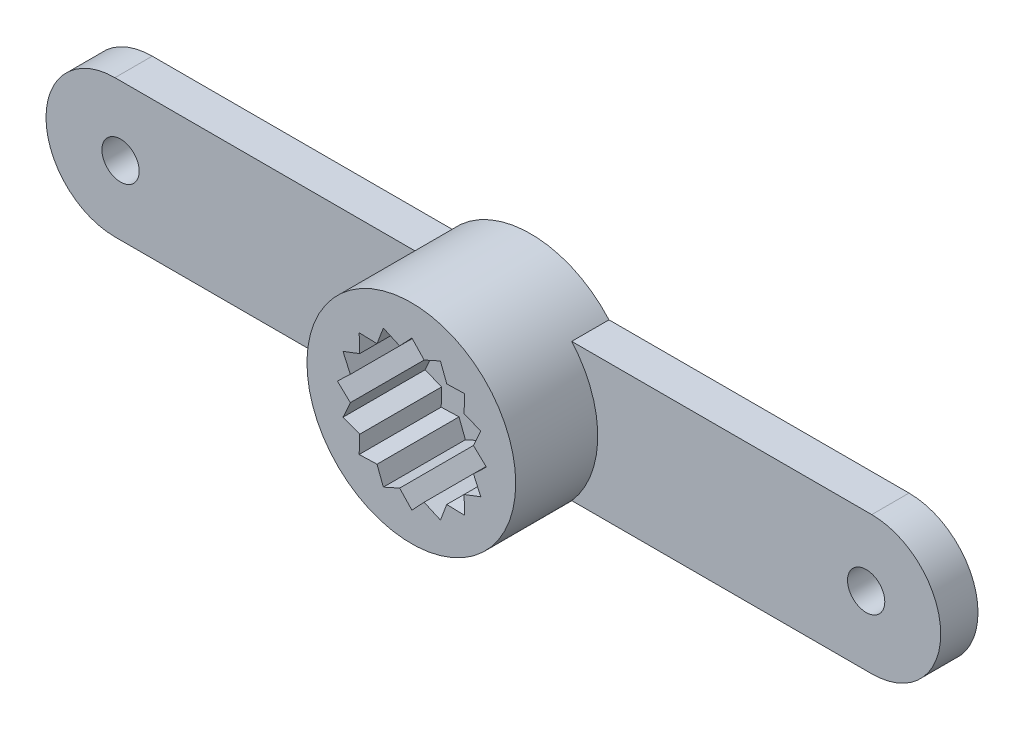
SolidWorks part; units mm, degrees
ref_plane "Front Plane" through (0, 0, 0) normal (0, 0, 1) x (1, 0, 0)
ref_plane "Top Plane" through (0, 0, 0) normal (0, 1, 0) x (1, 0, 0)
ref_plane "Right Plane" through (0, 0, 0) normal (1, 0, 0) x (0, 0, -1)
sketch "Sketch1" plane through (0, 0, 0) normal (0, 0, 1) x (1, 0, 0)
  circle A0 centre (0, 0) radius 2.8
  dimension "D1" = 5.6
extrude "Boss-Extrude1" add sketch "Sketch1" along normal blind 3.2
sketch "Sketch2" plane through (0, 0, 3.2) normal (0, 0, 1) x (1, 0, 0)
  line L0 (0.0147, -0.0147) -> (0.0147, 1.9853) construction
  line L1 (0.0147, -0.0147) -> (0.3432, 1.637) construction
  line L2 (0.0147, -0.0147) -> (-0.3139, 1.637) construction
  line L3 (0.0147, 1.9853) -> (-0.3139, 1.637)
  line L4 (0.0147, 1.9853) -> (0.3432, 1.637)
  line L5 (0.78, 1.8331) -> (0.9502, 1.3855)
  line L6 (0.78, 1.8331) -> (0.3432, 1.637)
  line L7 (1.4289, 1.3996) -> (1.4148, 0.9209)
  line L8 (1.4289, 1.3996) -> (0.9502, 1.3855)
  line L9 (1.8624, 0.7507) -> (1.6663, 0.3139)
  line L10 (1.8624, 0.7507) -> (1.4148, 0.9209)
  line L11 (2.0147, -0.0147) -> (1.6663, -0.3432)
  line L12 (2.0147, -0.0147) -> (1.6663, 0.3139)
  line L13 (1.8624, -0.78) -> (1.4148, -0.9502)
  line L14 (1.8624, -0.78) -> (1.6663, -0.3432)
  line L15 (1.4289, -1.4289) -> (0.9502, -1.4148)
  line L16 (1.4289, -1.4289) -> (1.4148, -0.9502)
  line L17 (0.78, -1.8624) -> (0.3432, -1.6663)
  line L18 (0.78, -1.8624) -> (0.9502, -1.4148)
  line L19 (0.0147, -2.0147) -> (-0.3139, -1.6663)
  line L20 (0.0147, -2.0147) -> (0.3432, -1.6663)
  line L21 (-0.7507, -1.8624) -> (-0.9209, -1.4148)
  line L22 (-0.7507, -1.8624) -> (-0.3139, -1.6663)
  line L23 (-1.3996, -1.4289) -> (-1.3855, -0.9502)
  line L24 (-1.3996, -1.4289) -> (-0.9209, -1.4148)
  line L25 (-1.8331, -0.78) -> (-1.637, -0.3432)
  line L26 (-1.8331, -0.78) -> (-1.3855, -0.9502)
  line L27 (-1.9853, -0.0147) -> (-1.637, 0.3139)
  line L28 (-1.9853, -0.0147) -> (-1.637, -0.3432)
  line L29 (-1.8331, 0.7507) -> (-1.3855, 0.9209)
  line L30 (-1.8331, 0.7507) -> (-1.637, 0.3139)
  line L31 (-1.3996, 1.3996) -> (-0.9209, 1.3855)
  line L32 (-1.3996, 1.3996) -> (-1.3855, 0.9209)
  line L33 (-0.7507, 1.8331) -> (-0.3139, 1.637)
  line L34 (-0.7507, 1.8331) -> (-0.9209, 1.3855)
extrude "Cut-Extrude1" cut sketch "Sketch2" against normal blind 2.2
sketch "Sketch3" plane through (0, 0, 0) normal (0, 0, 1) x (1, 0, 0)
  circle A1 centre (0, 0) radius 0.75
  dimension "D1" = 1.5
extrude "Cut-Extrude2" cut sketch "Sketch3" along normal blind 1
sketch "Sketch4" plane through (0, 0, 0) normal (0, 0, 1) x (1, 0, 0)
  line L0 (0, -2.8) -> (0, 2.8) construction
  line L1 (10.15, 1.85) -> (-10.15, 1.85) construction
  line L2 (10.15, -1.85) -> (-10.15, -1.85) construction
  line L3 (-10.15, 1.85) -> (-10.15, -1.85) construction
  line L4 (-0.75, 1.85) -> (-0.75, -1.85)
  line L5 (0, -1.85) -> (-0.0802, -1.9054)
  line L6 (0.75, 0) -> (-0.75, 0) construction
  line L7 (-0.75, 1.85) -> (-10.15, 1.85)
  line L8 (-10.15, -1.85) -> (-0.75, -1.85)
  line L9 (10.15, 1.85) -> (10.15, -1.85) construction
  line L10 (10.15, -1.85) -> (0.75, -1.85)
  line L11 (0.75, 1.85) -> (10.15, 1.85)
  line L12 (0.75, 1.85) -> (0.75, -1.85)
  circle A0 centre (0, 0) radius 2.8 construction
  arc A1 (-10.15, 1.85) -> (-10.15, -1.85) centre (-10.15, 0) ccw
  circle A2 centre (0, 0) radius 0.75 construction
  arc A3 (10.15, 1.85) -> (10.15, -1.85) centre (10.15, 0) cw
  point P19 (0, 0)
  point P21 (0, 1.85)
  dimension "D1" = 3.7
  dimension "D2" = 1.85
  dimension "D3" = 10.15
extrude "Boss-Extrude2" add sketch "Sketch4" along normal blind 1 contours A3 L11 L12 L10 | L7 A1 L8 L4
sketch "Sketch5" plane through (0, 0, 0) normal (0, 0, -1) x (-1, 0, 0)
  line L0 (0, 0) -> (14.3906, 0) construction
  line L1 (0, -5.9427) -> (0, 5.9427) construction
  circle A0 centre (10, 0) radius 0.5
  circle A1 centre (-10, 0) radius 0.5
  dimension "D1" = 10
extrude "Cut-Extrude3" cut sketch "Sketch5" against normal up to next
equation "\"D2@Sketch4\" = \"D1@Sketch4\"/2"
